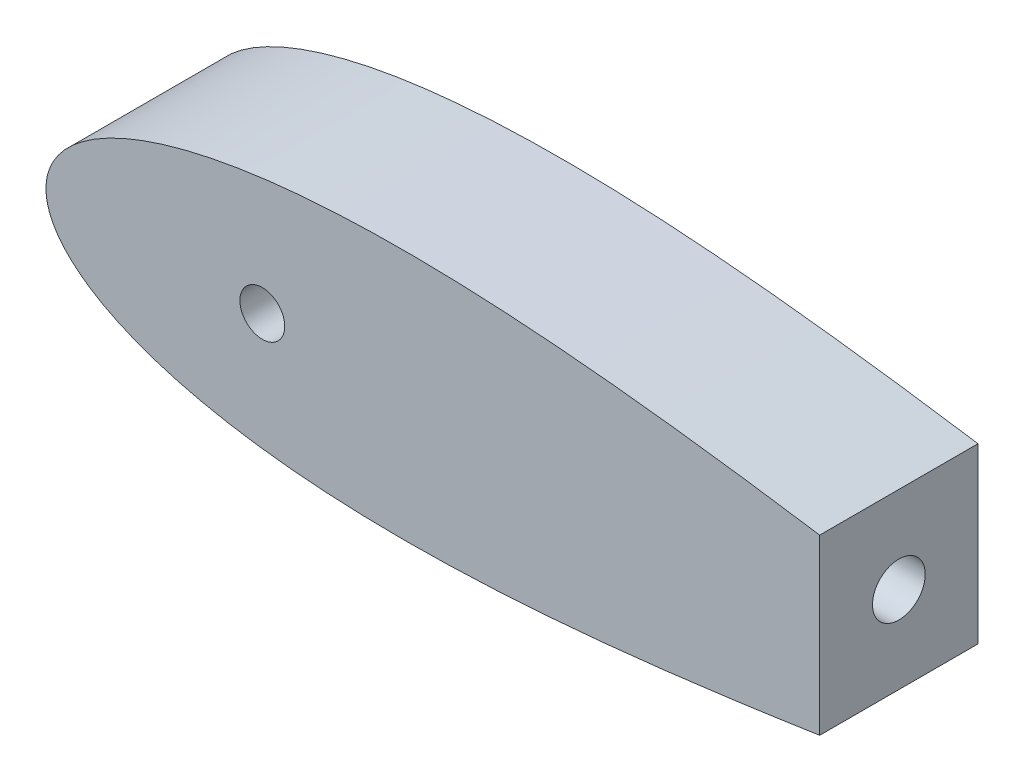
SolidWorks part; units mm, degrees
ref_plane "Front Plane" through (0, 0, 0) normal (0, 0, 1) x (1, 0, 0)
ref_plane "Top Plane" through (0, 0, 0) normal (0, 1, 0) x (1, 0, 0)
ref_plane "Right Plane" through (0, 0, 0) normal (1, 0, 0) x (0, 0, -1)
sketch "Sketch1" plane through (0, 0, 0) normal (0, 0, 1) x (1, 0, 0)
  line L0 (100, 0) -> (0, 0) construction
  line L1 (1.2169, -991.9959) -> (1.2169, 49008.0041) construction
  line L2 (93.345, 0) -> (114.935, 0) construction
  line L3 (125.634, 0) -> (131.6629, 0) construction
  line L4 (643.5991, 0) -> (643.5991, -1.016)
  line L9 (0, 0) -> (643.9668, 0)
  line L13 (460.661, 0) -> (473.361, 0)
  circle A0 centre (104.14, 0) radius 10.795 construction
  arc A1 (1.2169, -4.6585) -> (1.2169, 4.6585) centre (9.525, 0) cw
  arc A2 (641.5671, 0) -> (644.1071, 0) centre (642.8371, 0) ccw
  circle A4 centre (104.14, 0) radius 10.795
  circle A9 centre (40.64, 0) radius 12.7
  circle A14 centre (642.3793, 0) radius 1.5875 construction
  arc A15 (642.5108, -1.582) -> (642.5108, 1.582) centre (642.3793, 0) ccw
  spline S2 degree 3 poles (666.3448, -0.0547) (672.2538, 0) (666.3448, 0.0547) (662.8509, 0.2344) (656.505, 0.5436) (649.293, 1.0348) (640.4916, 1.7319) (630.4138, 2.6634) (619.0141, 3.8493) (606.375, 5.3044) (592.5439, 7.0376) (577.5855, 9.0506) (561.5643, 11.3389) (544.5497, 13.8907) (526.6141, 16.6877) (507.8326, 19.7051) (488.2827, 22.9117) (468.0444, 26.2704) (447.1994, 29.739) (425.8316, 33.2703) (404.0263, 36.8132) (381.8707, 40.3133) (359.4533, 43.7135) (336.8645, 46.9554) (314.1962, 49.9798) (291.5418, 52.7277) (268.9963, 55.1412) (246.6566, 57.1646) (224.6209, 58.7452) (202.9892, 59.8341) (181.8631, 60.3875) (161.3458, 60.367) (141.542, 59.7399) (122.5581, 58.4818) (104.5023, 56.5743) (87.485, 54.0089) (71.6197, 50.7848) (57.0237, 46.9125) (43.8205, 42.415) (32.1416, 37.3322) (22.1291, 31.7315) (13.9324, 25.7264) (7.6896, 19.5132) (3.4631, 13.4204) (1.1063, 7.9234) (0.1546, 3.5138) (-0.0622, 0) (0.1546, -3.5138) (1.1063, -7.9234) (3.4631, -13.4204) (7.6896, -19.5132) (13.9324, -25.7264) (22.1291, -31.7315) (32.1416, -37.3322) (43.8205, -42.415) (57.0237, -46.9125) (71.6197, -50.7848) (87.485, -54.0089) (104.5023, -56.5743) (122.5581, -58.4818) (141.542, -59.7399) (161.3458, -60.367) (181.8631, -60.3875) (202.9892, -59.8341) (224.6209, -58.7452) (246.6566, -57.1646) (268.9963, -55.1412) (291.5418, -52.7277) (314.1962, -49.9798) (336.8645, -46.9554) (359.4533, -43.7135) (381.8707, -40.3133) (404.0263, -36.8132) (425.8316, -33.2703) (447.1994, -29.739) (468.0444, -26.2704) (488.2827, -22.9117) (507.8326, -19.7051) (526.6141, -16.6877) (544.5497, -13.8907) (561.5643, -11.3389) (577.5855, -9.0506) (592.5439, -7.0376) (606.375, -5.3044) (619.0141, -3.8493) (630.4138, -2.6634) (640.4916, -1.7319) (649.293, -1.0348) (656.505, -0.5436) (662.8509, -0.2344) (666.3448, -0.0547) (672.2538, 0) (666.3448, 0.0547) knots -0.009667 -0.005395 -0.002168 0 0.002168 0.005395 0.009667 0.014967 0.021271 0.028553 0.036781 0.04592 0.055932 0.066773 0.078397 0.090755 0.103793 0.117456 0.131686 0.146422 0.1616 0.177156 0.193024 0.209135 0.225421 0.241812 0.258238 0.274629 0.290914 0.307025 0.322893 0.338448 0.353626 0.368361 0.38259 0.396253 0.40929 0.421647 0.43327 0.444109 0.454119 0.463255 0.471479 0.478755 0.485052 0.490344 0.49461 0.497833 0.5 0.502167 0.50539 0.509656 0.514948 0.521245 0.528521 0.536745 0.545881 0.555891 0.56673 0.578353 0.59071 0.603747 0.61741 0.631639 0.646374 0.661552 0.677107 0.692975 0.709086 0.725371 0.741762 0.758188 0.774579 0.790865 0.806976 0.822844 0.8384 0.853578 0.868314 0.882544 0.896207 0.909245 0.921603 0.933227 0.944068 0.95408 0.963219 0.971447 0.978729 0.985033 0.990333 0.994605 0.997832 1 1.002168 1.005395 1.009667 only from (670.56, 0) to (670.56, 0)
  point P2 (167.64, 0)
  point P8 (1.2169, -4.6585)
  point P10 (1.2169, 4.6585)
  point P28 (133.9182, 0)
  point P49 (130.0977, 0)
  point P59 (95.1064, 0)
  dimension "D2" = 21.59
  dimension "D3" = 1.016
  dimension "D4" = 1.27
  dimension "D8" = 25.4
  dimension "D9" = 63.5
  dimension "D10" = 3.175
  dimension "D6" = 63.5
extrude "Boss-Extrude1" add sketch "Sketch1" along normal blind 76.2 contours S2
sketch "Sketch3" plane through (0, 0, 76.2) normal (0, 0, 1) x (1, 0, 0)
  circle A0 centre (104.1392, 0) radius 10.795
  dimension "D1" = 21.59
extrude "Cut-Extrude2" cut sketch "Sketch3" against normal blind 76.2
sketch "Sketch4" plane through (0, 0, 76.2) normal (0, 0, 1) x (1, 0, 0)
sketch "Sketch6" plane through (0, 0, 0) normal (1, 0, 0) x (0, 0, -1)
  circle A0 centre (-20.32, 0) radius 6.35
  dimension "D1" = 12.7
  dimension "D2" = 20.32
extrude "Cut-Extrude3" cut sketch "Sketch6" against normal blind 0.0003 and the other way blind 53.34
sketch "Sketch7" plane through (0, 0, 0) normal (0, 0, -1) x (-1, 0, 0)
  circle A0 centre (-38.1, 0) radius 1.5875
  circle A1 centre (-50.8, 0) radius 1.5875
  point P4 (0, 0)
  dimension "D1" = 3.175
  dimension "D2" = 3.175
  dimension "D3" = 12.7
  dimension "D4" = 38.1
extrude "Cut-Extrude4" cut sketch "Sketch7" against normal blind 30.48
sketch "Sketch8" plane through (0, 0, 0) normal (0, 0, -1) x (-1, 0, 0)
  line L1 (-677.2433, 63.9901) -> (-372.4433, 63.9901)
  line L2 (-677.2433, 63.9901) -> (-677.2433, -63.0099)
  line L3 (-677.2433, -63.0099) -> (-372.4433, -63.0099)
  line L4 (-372.4433, 63.9901) -> (-372.4433, -63.0099)
  dimension "D1" = 127
  dimension "D2" = 372.4433
  dimension "D3" = 304.8
extrude "Cut-Extrude5" cut sketch "Sketch8" against normal blind 76.2
sketch "Sketch9" plane through (372.4433, 0, 0) normal (1, 0, 0) x (0, 0, -1)
  line L0 (0, -41.7363) -> (0, 41.7363) construction
  circle A0 centre (-38.1, 0) radius 12.7
  dimension "D1" = 25.4
  dimension "D2" = 38.1
extrude "Cut-Extrude6" cut sketch "Sketch9" against normal blind 101.6 contours A0
sketch "Sketch10" plane through (0, 0, 0) normal (0, 0, -1) x (-1, 0, 0)
  line L0 (-372.4433, -41.7363) -> (-372.4433, 41.7363) construction
  circle A0 centre (-343.8683, 0) radius 3.175
  circle A1 centre (-286.7183, 0) radius 3.175
  dimension "D1" = 57.15
  dimension "D2" = 28.575
  dimension "D3" = 6.35
  dimension "D4" = 6.35
extrude "Cut-Extrude7" cut sketch "Sketch10" against normal blind 57.15
